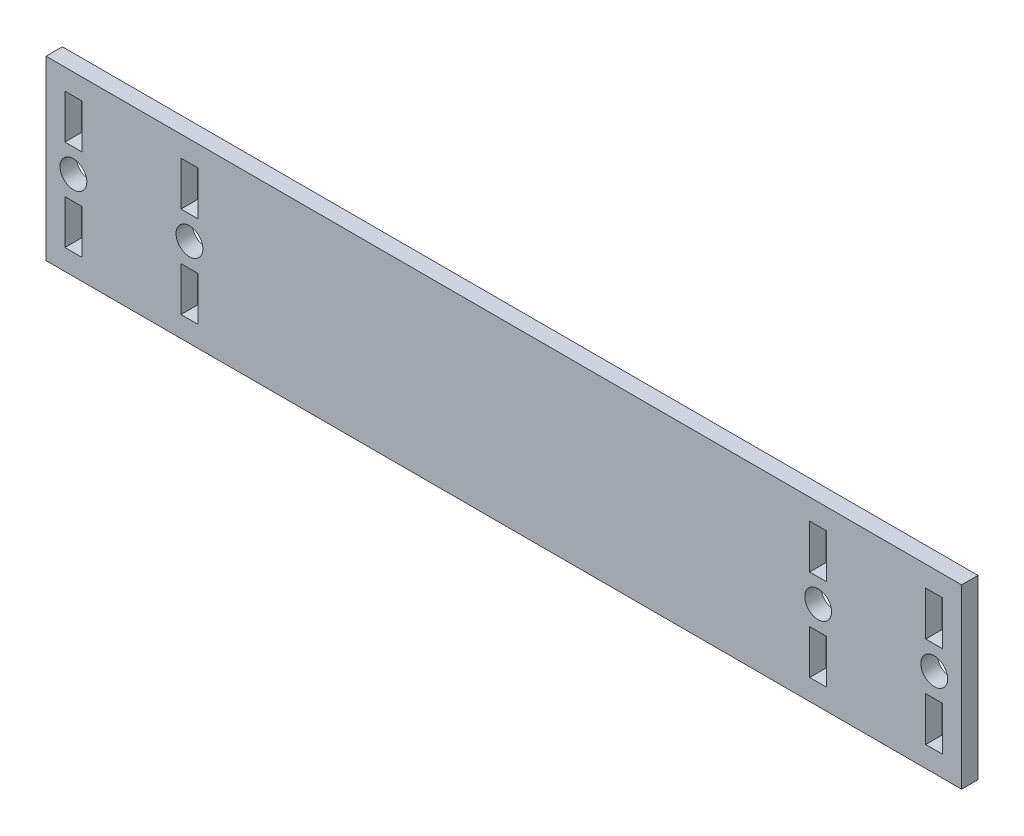
SolidWorks part; units mm, degrees
ref_plane "Front Plane" through (0, 0, 0) normal (0, 0, 1) x (1, 0, 0)
ref_plane "Top Plane" through (0, 0, 0) normal (0, 1, 0) x (1, 0, 0)
ref_plane "Right Plane" through (0, 0, 0) normal (1, 0, 0) x (0, 0, -1)
sketch "Sketch1" plane through (0, 0, 0) normal (0, 0, 1) x (1, 0, 0)
  line L0 (-92.2939, 0) -> (92.2939, 0) construction
  line L1 (92.2939, 17.8435) -> (-92.2939, 17.8435)
  line L2 (92.2939, 17.8435) -> (92.2939, -17.8435)
  line L3 (92.2939, -17.8435) -> (-92.2939, -17.8435)
  line L4 (-92.2939, 17.8435) -> (-92.2939, -17.8435)
  line L5 (92.2939, 17.8435) -> (-92.2939, -17.8435) construction
  line L6 (92.2939, -17.8435) -> (-92.2939, 17.8435) construction
  line L7 (-86.7694, 4.7625) -> (-86.7694, -4.7625) construction
  line L8 (-88.4839, 13.6525) -> (-85.0549, 13.6525)
  line L9 (-88.4839, 13.6525) -> (-88.4839, 4.7625)
  line L10 (-88.4839, 4.7625) -> (-85.0549, 4.7625)
  line L11 (-85.0549, 13.6525) -> (-85.0549, 4.7625)
  line L12 (-88.4839, 13.6525) -> (-85.0549, 4.7625) construction
  line L13 (-88.4839, 4.7625) -> (-85.0549, 13.6525) construction
  line L14 (-88.4839, -4.7625) -> (-85.0549, -4.7625)
  line L15 (-88.4839, -4.7625) -> (-88.4839, -13.6525)
  line L16 (-88.4839, -13.6525) -> (-85.0549, -13.6525)
  line L17 (-85.0549, -4.7625) -> (-85.0549, -13.6525)
  line L18 (-88.4839, -4.7625) -> (-85.0549, -13.6525) construction
  line L19 (-88.4839, -13.6525) -> (-85.0549, -4.7625) construction
  line L20 (-65.0849, 4.7625) -> (-61.6559, 4.7625)
  line L21 (-65.0849, 13.6525) -> (-61.6559, 13.6525)
  line L22 (-65.0849, 13.6525) -> (-61.6559, 4.7625) construction
  line L23 (-65.0849, 13.6525) -> (-65.0849, 4.7625)
  line L24 (-65.0849, -13.6525) -> (-61.6559, -13.6525)
  line L25 (-65.0849, -4.7625) -> (-61.6559, -4.7625)
  line L26 (-61.6559, 13.6525) -> (-61.6559, 4.7625)
  line L27 (-65.0849, 4.7625) -> (-61.6559, 13.6525) construction
  line L28 (-61.6559, -4.7625) -> (-61.6559, -13.6525)
  line L29 (-65.0849, -13.6525) -> (-61.6559, -4.7625) construction
  line L30 (-65.0849, -4.7625) -> (-65.0849, -13.6525)
  line L31 (-63.3704, 4.7625) -> (-63.3704, -4.7625) construction
  line L32 (-65.0849, -4.7625) -> (-61.6559, -13.6525) construction
  line L33 (0, 17.8435) -> (0, -17.8435) construction
  line L34 (65.0849, -4.7625) -> (61.6559, -13.6525) construction
  line L35 (63.3704, 4.7625) -> (63.3704, -4.7625) construction
  line L36 (65.0849, -13.6525) -> (61.6559, -4.7625) construction
  line L37 (65.0849, 4.7625) -> (61.6559, 13.6525) construction
  line L38 (65.0849, 13.6525) -> (61.6559, 4.7625) construction
  line L39 (88.4839, -13.6525) -> (85.0549, -4.7625) construction
  line L40 (88.4839, -4.7625) -> (85.0549, -13.6525) construction
  line L41 (88.4839, 4.7625) -> (85.0549, 13.6525) construction
  line L42 (88.4839, 13.6525) -> (85.0549, 4.7625) construction
  line L43 (86.7694, 4.7625) -> (86.7694, -4.7625) construction
  line L44 (65.0849, -4.7625) -> (65.0849, -13.6525)
  line L45 (61.6559, -4.7625) -> (61.6559, -13.6525)
  line L46 (61.6559, 13.6525) -> (61.6559, 4.7625)
  line L47 (65.0849, -4.7625) -> (61.6559, -4.7625)
  line L48 (65.0849, -13.6525) -> (61.6559, -13.6525)
  line L49 (65.0849, 13.6525) -> (65.0849, 4.7625)
  line L50 (65.0849, 13.6525) -> (61.6559, 13.6525)
  line L51 (65.0849, 4.7625) -> (61.6559, 4.7625)
  line L52 (85.0549, -4.7625) -> (85.0549, -13.6525)
  line L53 (88.4839, -13.6525) -> (85.0549, -13.6525)
  line L54 (88.4839, -4.7625) -> (88.4839, -13.6525)
  line L55 (88.4839, -4.7625) -> (85.0549, -4.7625)
  line L56 (85.0549, 13.6525) -> (85.0549, 4.7625)
  line L57 (88.4839, 4.7625) -> (85.0549, 4.7625)
  line L58 (88.4839, 13.6525) -> (88.4839, 4.7625)
  line L59 (88.4839, 13.6525) -> (85.0549, 13.6525)
  circle A0 centre (-86.7694, 0) radius 2.704
  circle A1 centre (-63.3704, 0) radius 2.704
  circle A2 centre (63.3704, 0) radius 2.704
  circle A3 centre (86.7694, 0) radius 2.704
  point P0 (0, 0)
  point P8 (-86.7694, 9.2075)
  point P13 (-86.7694, -9.2075)
  point P18 (-86.7694, 0)
  point P21 (-63.3704, 9.2075)
  point P26 (-63.3704, -9.2075)
  point P56 (63.3704, -9.2075)
  point P57 (63.3704, 9.2075)
  point P58 (86.7694, -9.2075)
  point P59 (86.7694, 9.2075)
  dimension "D8" = 5.408
  dimension "D1" = 35.687
  dimension "D2" = 184.5879
  dimension "D3" = 8.89
  dimension "D4" = 3.429
  dimension "D5" = 3.81
  dimension "D6" = 27.305
  dimension "D7" = 19.97
extrude "Boss-Extrude1" add sketch "Sketch1" along normal blind 3.302
